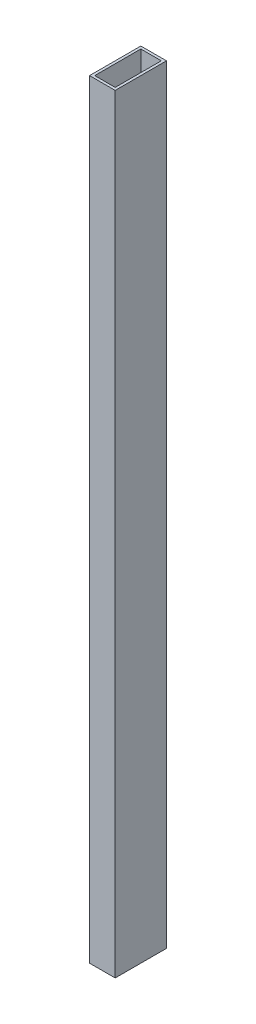
SolidWorks part; units mm, degrees
ref_plane "Спереди" through (0, 0, 0) normal (0, 0, 1) x (1, 0, 0)
ref_plane "Сверху" through (0, 0, 0) normal (0, 1, 0) x (1, 0, 0)
ref_plane "Справа" through (0, 0, 0) normal (1, 0, 0) x (0, 0, -1)
sketch "Sketch1" plane through (0, 0, 0) normal (0, 1, 0) x (1, 0, 0)
  line L1 (5, -10) -> (-5, -10)
  line L2 (5, -10) -> (5, 10)
  line L3 (5, 10) -> (-5, 10)
  line L4 (-5, -10) -> (-5, 10)
  line L5 (5, -10) -> (-5, 10) construction
  line L6 (5, 10) -> (-5, -10) construction
  line L7 (4, -9) -> (-4, -9)
  line L8 (4, -9) -> (4, 9)
  line L9 (4, 9) -> (-4, 9)
  line L10 (-4, -9) -> (-4, 9)
  line L11 (4, -9) -> (-4, 9) construction
  line L12 (4, 9) -> (-4, -9) construction
  point P0 (0, 0)
  point P6 (0, 0)
  dimension "D1" = 10
  dimension "D2" = 20
  dimension "D3" = 1
  dimension "D4" = 1
extrude "Boss-Extrude1" add sketch "Sketch1" along normal blind 300
